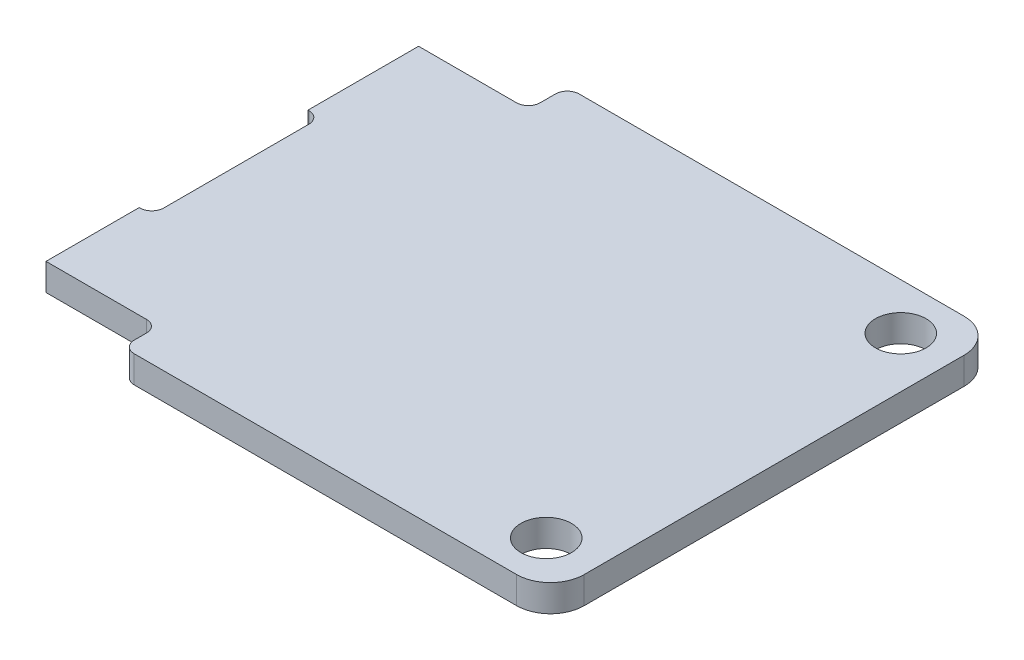
SolidWorks part; units mm, degrees
ref_plane "Front Plane" through (0, 0, 0) normal (0, 0, 1) x (1, 0, 0)
ref_plane "Top Plane" through (0, 0, 0) normal (0, 1, 0) x (1, 0, 0)
ref_plane "Right Plane" through (0, 0, 0) normal (1, 0, 0) x (0, 0, -1)
sketch "Sketch1" plane through (0, 0, 0) normal (0, 1, 0) x (1, 0, 0)
  line L0 (-9.7021, 11.6421) -> (-9.7021, 12.55)
  line L1 (-8.8503, -13.25) -> (13.7979, -13.25)
  line L2 (-16.2021, -11.1242) -> (-16.2021, -5.6044)
  line L3 (-9.0021, 13.25) -> (13.7979, 13.25)
  line L4 (15.7979, -11.25) -> (15.7979, 11.25)
  line L5 (-13.2634, -11.1242) -> (15.7979, 13.25) construction
  line L6 (-16.2021, 4.3956) -> (-16.2021, 10.9421)
  line L7 (-10.2503, -11.1242) -> (-16.2021, -11.1242)
  line L9 (-10.4021, 10.9421) -> (-16.2021, 10.9421)
  line L10 (-16.2021, -11.1242) -> (-16.2021, -5.6044)
  line L11 (-16.1521, -5.6044) -> (-16.2021, -5.6044)
  line L12 (-15.4521, -4.9044) -> (-15.4521, 3.6956)
  line L13 (-9.5503, -11.8242) -> (-9.5503, -12.55)
  line L14 (-9.7021, 13.25) -> (-9.7021, 10.9421)
  line L15 (-0.119, -0.0998) -> (15.7979, -13.25) construction
  line L16 (-16.1521, 4.3956) -> (-16.2021, 4.3956)
  line L20 (-16.2021, 4.3956) -> (-16.2021, 10.9421)
  arc A0 (-9.7021, 12.55) -> (-9.0021, 13.25) centre (-9.0021, 12.55) cw
  arc A1 (-9.5503, -12.55) -> (-8.8503, -13.25) centre (-8.8503, -12.55) ccw
  arc A2 (-10.2503, -11.1242) -> (-9.5503, -11.8242) centre (-10.2503, -11.8242) cw
  arc A3 (-9.7021, 11.6421) -> (-10.4021, 10.9421) centre (-10.4021, 11.6421) cw
  circle A4 centre (12.7979, 10.5) radius 1.5
  circle A5 centre (12.7979, -10.5) radius 1.5
  arc A6 (13.7979, -13.25) -> (15.7979, -11.25) centre (13.7979, -11.25) ccw
  arc A7 (13.7979, 13.25) -> (15.7979, 11.25) centre (13.7979, 11.25) cw
  arc A8 (-16.1521, -5.6044) -> (-15.4521, -4.9044) centre (-16.1521, -4.9044) ccw
  arc A9 (-15.4521, 3.6956) -> (-16.1521, 4.3956) centre (-16.1521, 3.6956) ccw
  point P0 (0, 0)
  point P6 (-12.75, 0)
  point P34 (-15.4521, -0.6044)
  point P40 (-15.4521, -5.6044)
  point P43 (-15.4521, 4.3956)
  dimension "D1" = 0.7
  dimension "D2" = 21
  dimension "D6" = 2
  dimension "D10" = 0.7
  dimension "D3" = 6.5
  dimension "D4" = 10.5
  dimension "D5" = 3
  dimension "D7" = 10
  dimension "D8" = 0.75
  dimension "D9" = 32
extrude "Boss-Extrude1" add sketch "Sketch1" along normal blind 1.6
